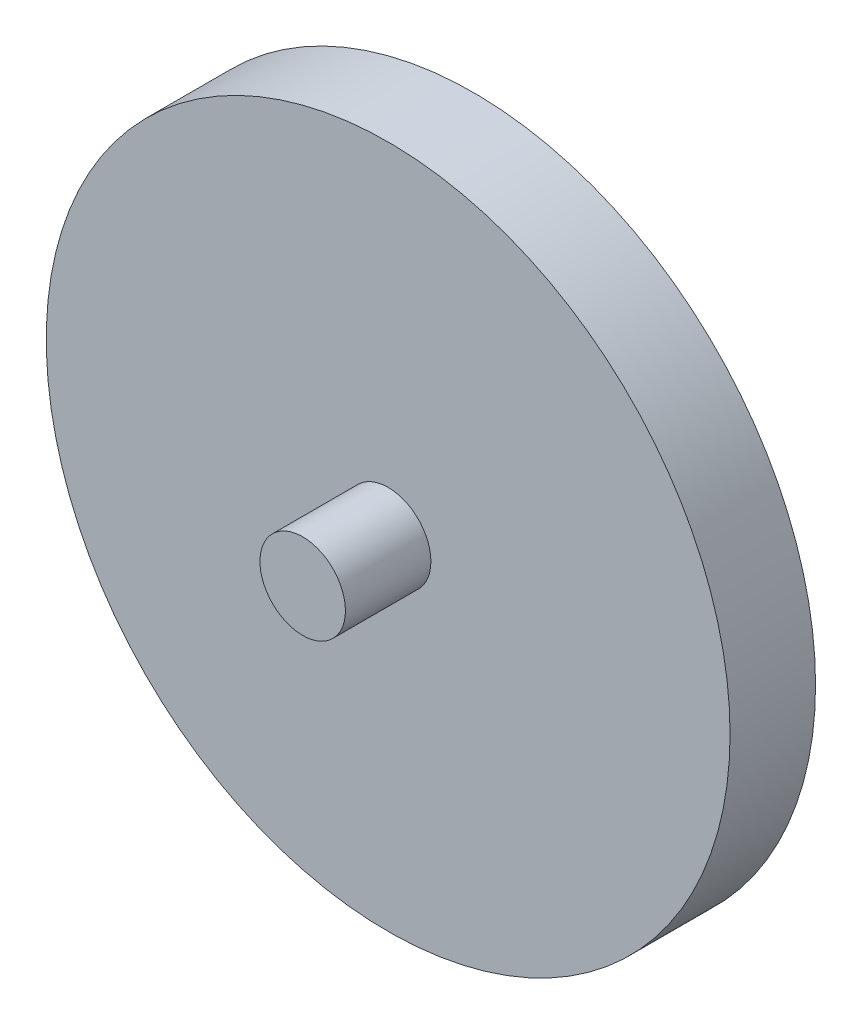
SolidWorks part; units mm, degrees
material "ABS"
ref_plane "Alzado" through (0, 0, 0) normal (0, 0, 1) x (1, 0, 0)
ref_plane "Planta" through (0, 0, 0) normal (0, 1, 0) x (1, 0, 0)
ref_plane "Vista lateral" through (0, 0, 0) normal (1, 0, 0) x (0, 0, -1)
sketch "Croquis2" plane through (0, 0, 0) normal (0, 0, 1) x (1, 0, 0)
  circle A0 centre (0, 0) radius 20
  dimension "D1" = 40
extrude "Saliente-Extruir2" add sketch "Croquis2" along normal blind 5
sketch "Croquis3" plane through (0, 0, 5) normal (0, 0, 1) x (1, 0, 0)
  circle A0 centre (0, 0) radius 2.5
  dimension "D1" = 5
extrude "Saliente-Extruir4" add sketch "Croquis3" along normal blind 5
